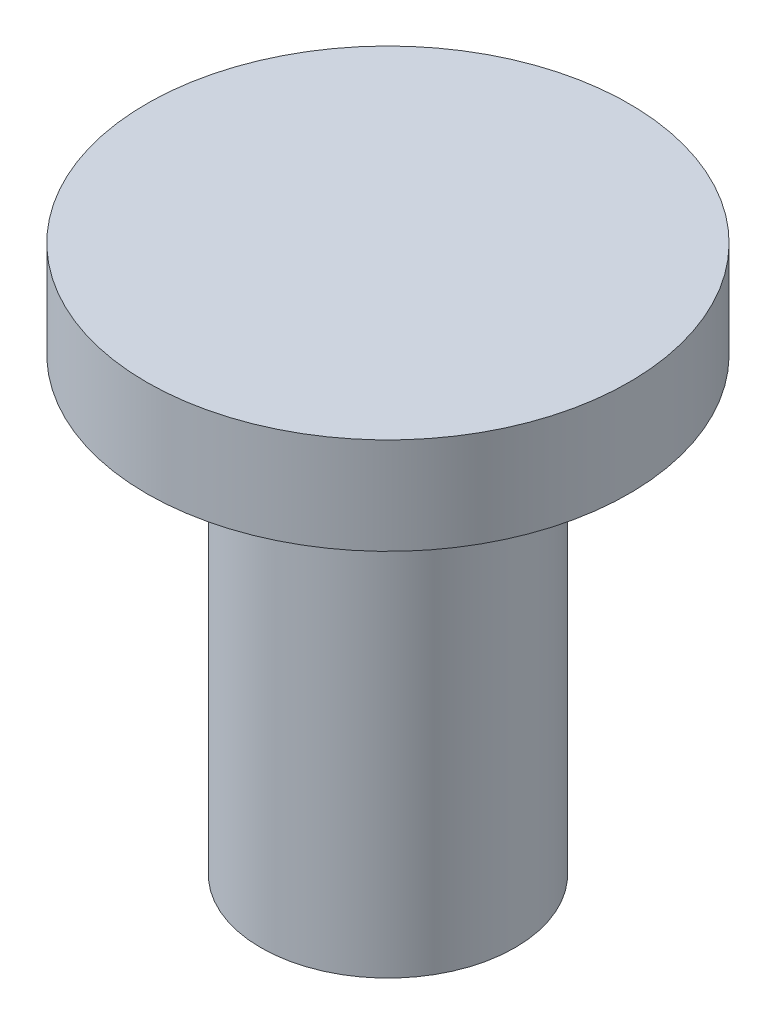
SolidWorks part; units mm, degrees
ref_plane "Front Plane" through (0, 0, 0) normal (0, 0, 1) x (1, 0, 0)
ref_plane "Top Plane" through (0, 0, 0) normal (0, 1, 0) x (1, 0, 0)
ref_plane "Right Plane" through (0, 0, 0) normal (1, 0, 0) x (0, 0, -1)
sketch "Sketch2" plane through (0, 0, 0) normal (1, 0, 0) x (0, 0, -1)
  line L0 (2.0525, 9.4227) -> (-5.4475, 9.4227)
  line L1 (-5.4475, 9.4227) -> (-5.4475, 6.4227)
  line L2 (-5.4475, 6.4227) -> (-1.8975, 6.4227)
  line L3 (-1.8975, 6.4227) -> (-1.8975, -7.5773)
  line L4 (-1.8975, -7.5773) -> (2.0525, -7.5773)
  line L5 (2.0525, 9.4227) -> (2.0525, -7.5773) construction
  line L6 (2.0525, 9.4227) -> (2.0525, -7.5773)
  dimension "D1" = 7.5
  dimension "D2" = 3
  dimension "D3" = 3.55
  dimension "D4" = 14
revolve "Revolve1" add sketch "Sketch2" angle 360 about L5
